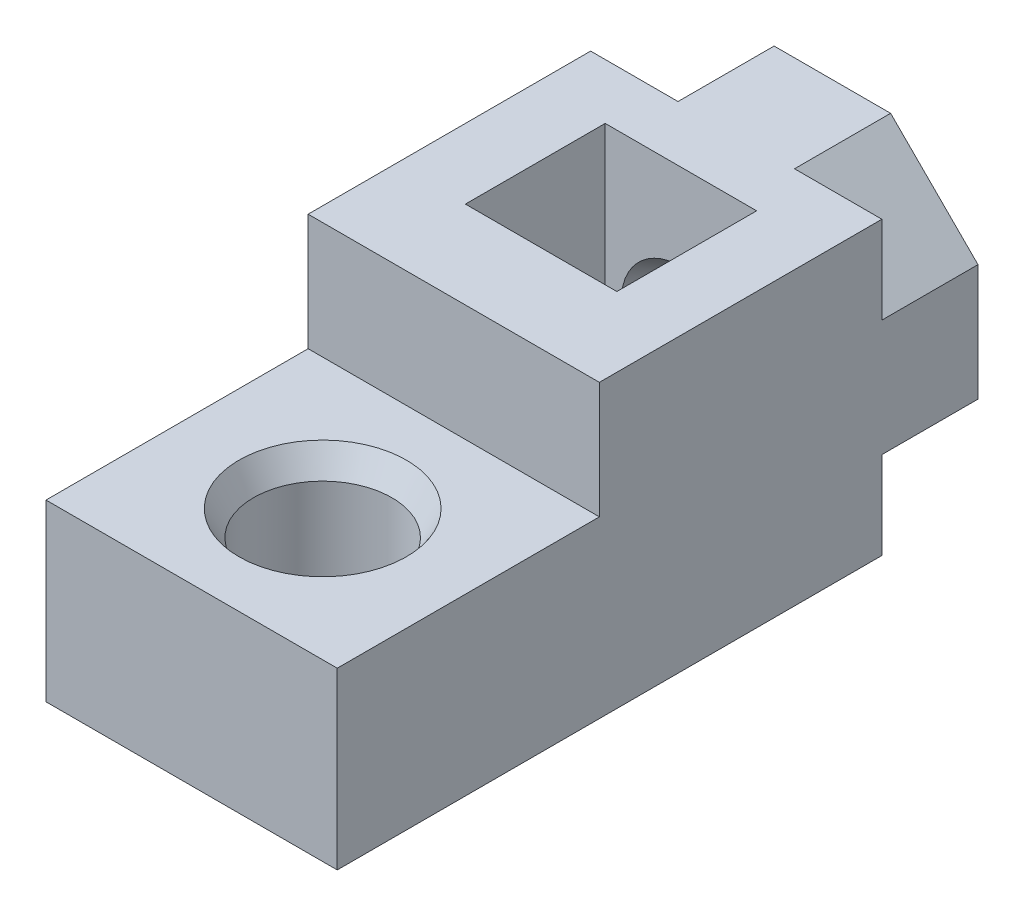
SolidWorks part; units mm, degrees
material "POM 乙缩醛共聚物"
ref_plane "前视基准面" through (0, 0, 0) normal (0, 0, 1) x (1, 0, 0)
ref_plane "上视基准面" through (0, 0, 0) normal (0, 1, 0) x (1, 0, 0)
ref_plane "右视基准面" through (0, 0, 0) normal (1, 0, 0) x (0, 0, -1)
sketch "草图1" plane through (0, 0, 0) normal (0, 0, 1) x (1, 0, 0)
  line L1 (-5, 5) -> (5, 5)
  line L2 (-5, 5) -> (-5, -5)
  line L3 (-5, -5) -> (5, -5)
  line L4 (5, 5) -> (5, -5)
  line L5 (-5, 5) -> (5, -5) construction
  line L6 (-5, -5) -> (5, 5) construction
  point P0 (0, 0)
  dimension "D1" = 10
  dimension "D2" = 10
extrude "凸台-拉伸1" add sketch "草图1" along normal blind 22
sketch "草图13" plane through (0, 0, 0) normal (0, 0, -1) x (-1, 0, 0)
  line L0 (2.6, 1.823) -> (2.6, 6)
  line L1 (2.6, -1.5011) -> (2.6, 1.823)
  line L4 (-2.6, 1.6542) -> (-2.6, -1.5011)
  line L5 (-2.6, -1.5011) -> (0, -3.0022)
  line L6 (0, -3.0022) -> (2.6, -1.5011)
  line L7 (2.6, 6) -> (-2.6, 6)
  line L8 (-2.6, 6) -> (-2.6, 1.6542)
  line L9 (-5, 5) -> (5, 5) construction
  line L10 (0.5242, 2.6996) -> (-0.8508, 3.4934) [skipped]
  line L11 (-0.5242, 2.6996) -> (-1.8992, 1.9057) [skipped]
  circle A0 centre (0, 0) radius 2.6 construction
  dimension "D1" = 5.2
  dimension "D2" = 1
extrude "切除-拉伸10" cut sketch "草图13" against normal blind 4.8 from offset 5.2 offset against normal yes
sketch "草图14" plane through (0, 0, 0) normal (0, 0, -1) x (-1, 0, 0)
  circle A0 centre (0, 0) radius 1.55
  dimension "D1" = 3.1
extrude "切除-拉伸11" cut sketch "草图14" against normal up to surface (10 mm away) up to face at (0, 0.7991, 10)
sketch "草图15" plane through (0, 5, 0) normal (0, 1, 0) x (1, 0, 0)
  line L0 (-5, -22) -> (-5, 0) construction
  line L1 (5, -22) -> (-5, -22)
  line L2 (5, -22) -> (5, -13)
  line L3 (5, -13) -> (-5, -13)
  line L4 (-5, -22) -> (-5, -13)
  line L5 (2.6, -10) -> (0, -10) construction
  dimension "D1" = 3
extrude "切除-拉伸12" cut sketch "草图15" against normal blind 4
sketch "草图16" plane through (0, 1, 0) normal (0, 1, 0) x (1, 0, 0)
  line L0 (5, -17.5) -> (-5, -17.5) construction
  line L1 (5, -22) -> (5, -13) construction
  line L2 (-5, -13) -> (-5, -22) construction
  line L3 (0, -22) -> (0, -13) construction
  line L4 (-5, -22) -> (5, -22) construction
  line L5 (5, -13) -> (-5, -13) construction
  circle A0 centre (0, -17.5) radius 2.375
  dimension "D1" = 4.75
extrude "切除-拉伸13" cut sketch "草图16" against normal through all
sketch "草图17" plane through (0, 0, 0) normal (0, 0, -1) x (-1, 0, 0)
  line L31 (5, 5) -> (2, 5)
  line L32 (-5, 5) -> (5, 5) construction
  line L33 (2, 5) -> (5, 2)
  line L34 (5, 5) -> (5, -5) construction
  line L35 (5, 2) -> (5, 5)
  line L36 (5, -5) -> (5, -2)
  line L37 (5, -2) -> (2, -5)
  line L39 (2, -5) -> (5, -5)
  line L40 (5, -5) -> (-5, -5) construction
  line L41 (-5, 5) -> (-5, 2)
  line L42 (-5, -5) -> (-5, 5) construction
  line L43 (-5, 2) -> (-2, 5)
  line L44 (-2, 5) -> (-5, 5)
  line L45 (-5, -5) -> (-2, -5)
  line L46 (-2, -5) -> (-5, -2)
  line L47 (-5, -2) -> (-5, -5)
  dimension "D1" = 3
  dimension "D2" = 3
  dimension "D3" = 3
  dimension "D4" = 3
  dimension "D5" = 3
  dimension "D6" = 3
  dimension "D7" = 3
  dimension "D8" = 3
extrude "切除-拉伸14" cut sketch "草图17" against normal blind 3.3
chamfer "倒角1" distance 0.5 angle 60 4 edges at (0, -5, 19.875) (0, 1, 19.875) (-1.55, 0, 5.2) (-1.55, 0, 0)
